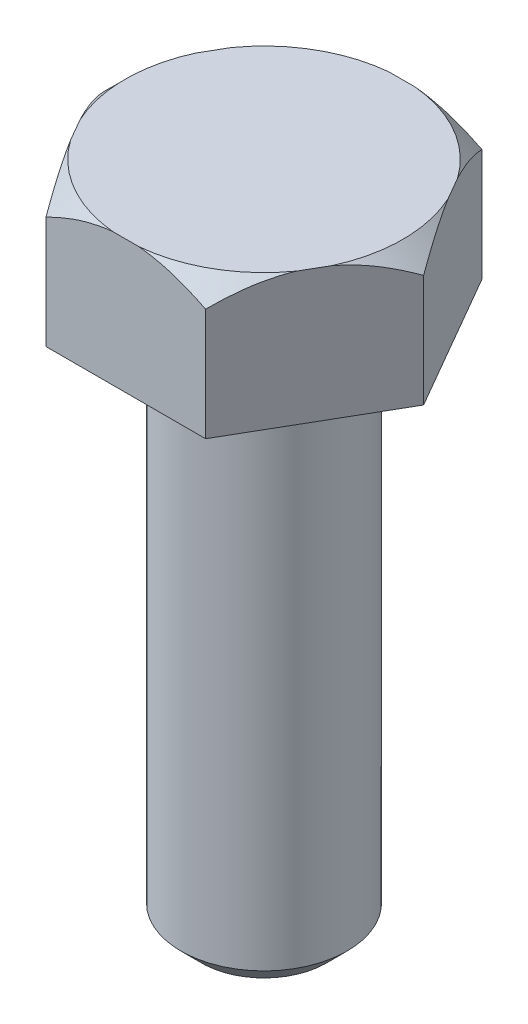
SolidWorks part; units mm, degrees
ref_plane "Front Plane" through (0, 0, 0) normal (0, 0, 1) x (1, 0, 0)
ref_plane "Top Plane" through (0, 0, 0) normal (0, 1, 0) x (1, 0, 0)
ref_plane "Right Plane" through (0, 0, 0) normal (1, 0, 0) x (0, 0, -1)
sketch "Sketch1" plane through (0, 0, 0) normal (0, 0, 1) x (1, 0, 0)
  line L0 (0, 0) -> (0, 12.7) construction
  line L1 (0, 12.7) -> (-2.6511, 12.7)
  line L2 (-3.048, 12.3031) -> (-3.048, 10.16)
  line L3 (-3.048, 10.16) -> (-1.5875, 10.16)
  line L4 (-1.5875, 10.16) -> (-1.5875, 0.3969)
  line L5 (-1.1906, 0) -> (0, 0)
  line L6 (-2.6511, 12.7) -> (-3.048, 12.3031)
  line L7 (-1.5875, 0.3969) -> (-1.1906, 0)
  line L8 (0, 0) -> (0, 12.7)
  point P4 (-3.048, 12.7)
  point P7 (-1.5875, 0)
  dimension "D1" = 12.7
  dimension "D2" = 1.5875
  dimension "D3" = 3.048
  dimension "D4" = 2.54
  dimension "D5" = 0.3969
  dimension "D6" = 45
  dimension "D7" = 0.3969
  dimension "D8" = 45
revolve "Revolve1" add sketch "Sketch1" angle 360 about L0
sketch "Sketch2" plane through (0, 12.7, 0) normal (0, 1, 0) x (1, 0, 0)
  line L1 (-1.524, 2.6396) -> (-3.048, 0)
  line L2 (-3.048, 0) -> (-1.524, -2.6396)
  line L3 (-1.524, -2.6396) -> (1.524, -2.6396)
  line L4 (1.524, -2.6396) -> (3.048, 0)
  line L5 (3.048, 0) -> (1.524, 2.6396)
  line L6 (1.524, 2.6396) -> (-1.524, 2.6396)
  circle A0 centre (0, 0) radius 2.6396 construction
  circle A1 centre (0, 0) radius 3.048 construction
extrude "Cut-Extrude1" cut sketch "Sketch2" against normal up to surface (2.54 mm away) flip side to cut up to face at (0, 10.16, -1.5875)
